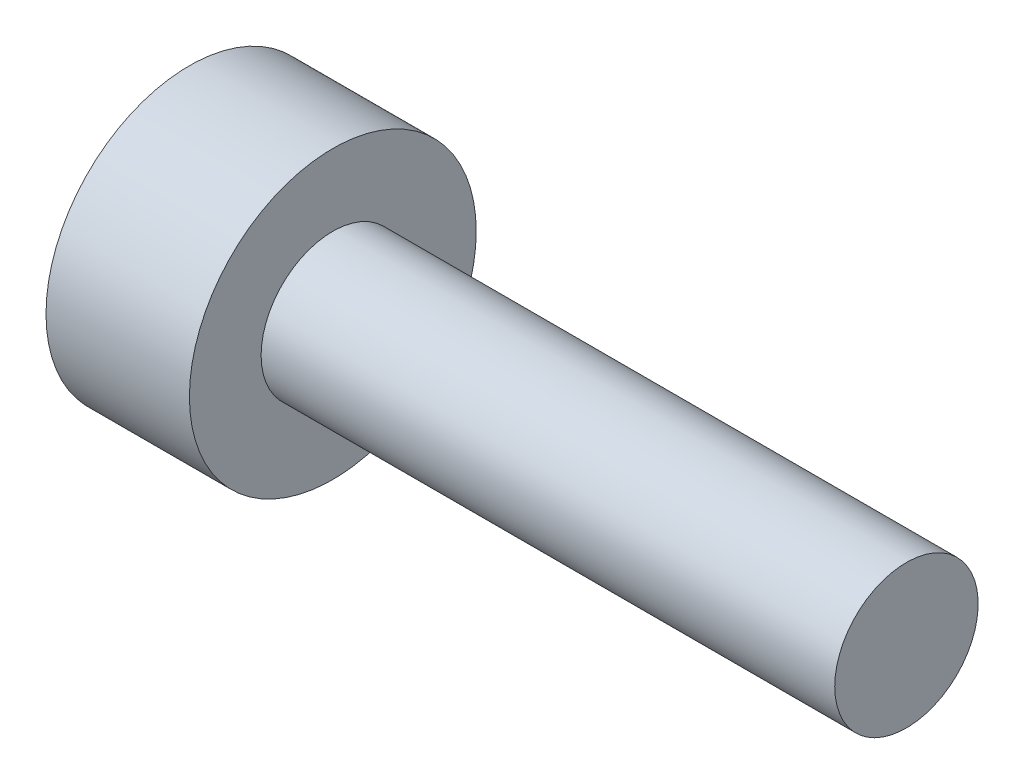
SolidWorks part; units mm, degrees
material "AISI Тип 316L нержавеющая сталь"
ref_plane "Спереди" through (0, 0, 0) normal (0, 0, 1) x (1, 0, 0)
ref_plane "Сверху" through (0, 0, 0) normal (0, 1, 0) x (1, 0, 0)
ref_plane "Справа" through (0, 0, 0) normal (1, 0, 0) x (0, 0, -1)
sketch "Эскиз1" plane through (0, 0, 0) normal (0, 0, 1) x (1, 0, 0)
  line L0 (0, 0) -> (0, 2)
  line L1 (0, 2) -> (2, 2)
  line L2 (2, 2) -> (2, 1)
  line L3 (2, 1) -> (10, 1)
  line L4 (10, 1) -> (10, 0)
  line L5 (10, 0) -> (0, 0)
  line L6 (0, 0) -> (12.0779, 0) construction
  dimension "D1" = 2
  dimension "D2" = 4
  dimension "D3" = 2
  dimension "D4" = 8
revolve "Повернуть1" add sketch "Эскиз1" angle 360 about L6
sketch "Эскиз2" plane through (0, 0, 0) normal (-1, 0, 0) x (0, 0, 1)
  line L1 (0.866, 0) -> (0.433, 0.75)
  line L2 (0.433, 0.75) -> (-0.433, 0.75)
  line L3 (-0.433, 0.75) -> (-0.866, 0)
  line L4 (-0.866, 0) -> (-0.433, -0.75)
  line L5 (-0.433, -0.75) -> (0.433, -0.75)
  line L6 (0.433, -0.75) -> (0.866, 0)
  circle A0 centre (0, 0) radius 0.75 construction
  dimension "D1" = 1.5
extrude "Вырез-Вытянуть1" cut sketch "Эскиз2" against normal blind 1.5
